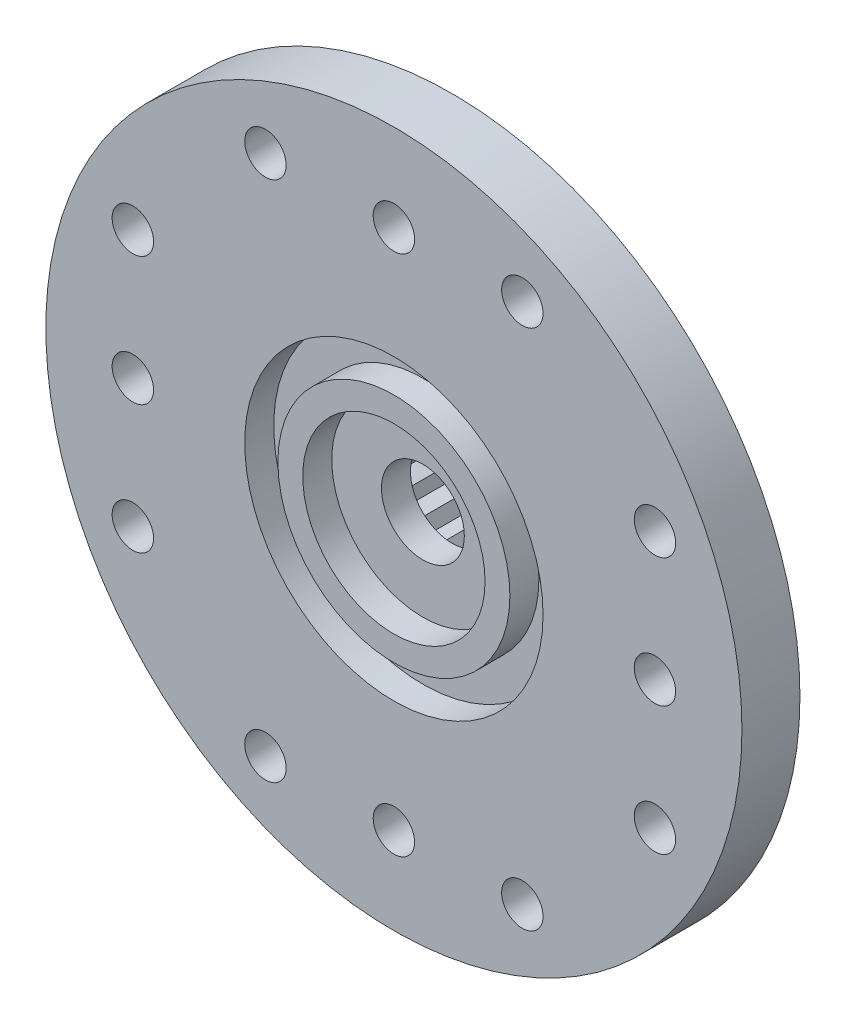
SolidWorks part; units mm, degrees
ref_plane "Front Plane" through (0, 0, 0) normal (0, 0, 1) x (1, 0, 0)
ref_plane "Top Plane" through (0, 0, 0) normal (0, 1, 0) x (1, 0, 0)
ref_plane "Right Plane" through (0, 0, 0) normal (1, 0, 0) x (0, 0, -1)
sketch "Sketch1" plane through (0, 0, 0) normal (0, 0, 1) x (1, 0, 0)
  line L50 (-10.25, 3) -> (-10.5946, 2.7283)
  line L51 (-10.5946, 2.7283) -> (-10.996, 2.9057)
  line L52 (-10.996, 2.9057) -> (-11.2623, 2.5569)
  line L53 (-11.2623, 2.5569) -> (-11.6952, 2.6289)
  line L54 (-11.6952, 2.6289) -> (-11.8664, 2.2248)
  line L55 (-11.8664, 2.2248) -> (-12.3036, 2.1869)
  line L56 (-12.3036, 2.1869) -> (-12.3689, 1.7529)
  line L57 (-12.3689, 1.7529) -> (-12.7829, 1.6075)
  line L58 (-12.7829, 1.6075) -> (-12.7382, 1.1709)
  line L59 (-12.7382, 1.1709) -> (-13.1031, 0.927)
  line L60 (-13.1031, 0.927) -> (-12.9512, 0.5153)
  line L61 (-12.9512, 0.5153) -> (-13.244, 0.1884)
  line L62 (-13.244, 0.1884) -> (-12.9945, -0.1727)
  line L63 (-12.9945, -0.1727) -> (-13.1968, -0.5621)
  line L64 (-13.1968, -0.5621) -> (-12.8654, -0.8498)
  line L65 (-12.8654, -0.8498) -> (-12.9644, -1.2773)
  line L66 (-12.9644, -1.2773) -> (-12.5719, -1.4735)
  line L67 (-12.5719, -1.4735) -> (-12.5615, -1.9123)
  line L68 (-12.5615, -1.9123) -> (-12.1325, -2.0047)
  line L69 (-12.1325, -2.0047) -> (-12.0133, -2.427)
  line L70 (-12.0133, -2.427) -> (-11.5748, -2.4098)
  line L71 (-11.5748, -2.4098) -> (-11.3543, -2.7893)
  line L72 (-11.3543, -2.7893) -> (-10.9339, -2.6636)
  line L73 (-10.9339, -2.6636) -> (-10.626, -2.9763)
  line L74 (-10.626, -2.9763) -> (-10.25, -2.75)
  line L75 (-10.25, -2.75) -> (-9.874, -2.9763)
  line L76 (-9.874, -2.9763) -> (-9.5661, -2.6636)
  line L77 (-9.5661, -2.6636) -> (-9.1456, -2.7893)
  line L78 (-9.1456, -2.7893) -> (-8.9251, -2.4098)
  line L79 (-8.9251, -2.4098) -> (-8.4866, -2.427)
  line L80 (-8.4866, -2.427) -> (-8.3675, -2.0047)
  line L81 (-8.3675, -2.0047) -> (-7.9384, -1.9123)
  line L82 (-7.9384, -1.9123) -> (-7.9281, -1.4735)
  line L83 (-7.9281, -1.4735) -> (-7.5355, -1.2773)
  line L84 (-7.5355, -1.2773) -> (-7.6346, -0.8498)
  line L85 (-7.6346, -0.8498) -> (-7.3031, -0.5621)
  line L86 (-7.3031, -0.5621) -> (-7.5054, -0.1727)
  line L87 (-7.5054, -0.1727) -> (-7.2559, 0.1884)
  line L88 (-7.2559, 0.1884) -> (-7.5487, 0.5153)
  line L89 (-7.5487, 0.5153) -> (-7.3968, 0.927)
  line L90 (-7.3968, 0.927) -> (-7.7617, 1.1709)
  line L91 (-7.7617, 1.1709) -> (-7.717, 1.6075)
  line L92 (-7.717, 1.6075) -> (-8.1311, 1.7529)
  line L93 (-8.1311, 1.7529) -> (-8.1963, 2.1869)
  line L94 (-8.1963, 2.1869) -> (-8.6336, 2.2248)
  line L95 (-8.6336, 2.2248) -> (-8.8047, 2.6289)
  line L96 (-8.8047, 2.6289) -> (-9.2376, 2.5569)
  line L97 (-9.2376, 2.5569) -> (-9.5039, 2.9057)
  line L98 (-9.5039, 2.9057) -> (-9.9053, 2.7283)
  line L99 (-9.9053, 2.7283) -> (-10.25, 3)
  line L100 (-10.25, 3) -> (-10.5946, 2.7283)
  line L101 (-10.5946, 2.7283) -> (-10.996, 2.9057)
  line L102 (-10.996, 2.9057) -> (-11.2623, 2.5569)
  line L103 (-11.2623, 2.5569) -> (-11.6952, 2.6289)
  line L104 (-11.6952, 2.6289) -> (-11.8664, 2.2248)
  line L105 (-11.8664, 2.2248) -> (-12.3036, 2.1869)
  line L106 (-12.3036, 2.1869) -> (-12.3689, 1.7529)
  line L107 (-12.3689, 1.7529) -> (-12.7829, 1.6075)
  line L108 (-12.7829, 1.6075) -> (-12.7382, 1.1709)
  line L109 (-12.7382, 1.1709) -> (-13.1031, 0.927)
  line L110 (-13.1031, 0.927) -> (-12.9512, 0.5153)
  line L111 (-12.9512, 0.5153) -> (-13.244, 0.1884)
  line L112 (-13.244, 0.1884) -> (-12.9945, -0.1727)
  line L113 (-12.9945, -0.1727) -> (-13.1968, -0.5621)
  line L114 (-13.1968, -0.5621) -> (-12.8654, -0.8498)
  line L115 (-12.8654, -0.8498) -> (-12.9644, -1.2773)
  line L116 (-12.9644, -1.2773) -> (-12.5719, -1.4735)
  line L117 (-12.5719, -1.4735) -> (-12.5615, -1.9123)
  line L118 (-12.5615, -1.9123) -> (-12.1325, -2.0047)
  line L119 (-12.1325, -2.0047) -> (-12.0133, -2.427)
  line L120 (-12.0133, -2.427) -> (-11.5748, -2.4098)
  line L121 (-11.5748, -2.4098) -> (-11.3543, -2.7893)
  line L122 (-11.3543, -2.7893) -> (-10.9339, -2.6636)
  line L123 (-10.9339, -2.6636) -> (-10.626, -2.9763)
  line L124 (-10.626, -2.9763) -> (-10.25, -2.75)
  line L125 (-10.25, -2.75) -> (-9.874, -2.9763)
  line L126 (-9.874, -2.9763) -> (-9.5661, -2.6636)
  line L127 (-9.5661, -2.6636) -> (-9.1456, -2.7893)
  line L128 (-9.1456, -2.7893) -> (-8.9251, -2.4098)
  line L129 (-8.9251, -2.4098) -> (-8.4866, -2.427)
  line L130 (-8.4866, -2.427) -> (-8.3675, -2.0047)
  line L131 (-8.3675, -2.0047) -> (-7.9384, -1.9123)
  line L132 (-7.9384, -1.9123) -> (-7.9281, -1.4735)
  line L133 (-7.9281, -1.4735) -> (-7.5355, -1.2773)
  line L134 (-7.5355, -1.2773) -> (-7.6346, -0.8498)
  line L135 (-7.6346, -0.8498) -> (-7.3031, -0.5621)
  line L136 (-7.3031, -0.5621) -> (-7.5054, -0.1727)
  line L137 (-7.5054, -0.1727) -> (-7.2559, 0.1884)
  line L138 (-7.2559, 0.1884) -> (-7.5487, 0.5153)
  line L139 (-7.5487, 0.5153) -> (-7.3968, 0.927)
  line L140 (-7.3968, 0.927) -> (-7.7617, 1.1709)
  line L141 (-7.7617, 1.1709) -> (-7.717, 1.6075)
  line L142 (-7.717, 1.6075) -> (-8.1311, 1.7529)
  line L143 (-8.1311, 1.7529) -> (-8.1963, 2.1869)
  line L144 (-8.1963, 2.1869) -> (-8.6336, 2.2248)
  line L145 (-8.6336, 2.2248) -> (-8.8047, 2.6289)
  line L146 (-8.8047, 2.6289) -> (-9.2376, 2.5569)
  line L147 (-9.2376, 2.5569) -> (-9.5039, 2.9057)
  line L148 (-9.5039, 2.9057) -> (-9.9053, 2.7283)
  line L149 (-9.9053, 2.7283) -> (-10.25, 3)
  circle A0 centre (-10.25, 0) radius 4.5
  dimension "D2" = 9
  dimension "D1" = 0
extrude "Boss-Extrude1" add sketch "Sketch1" against normal blind 3.75 contours A0 L149 L148 L147 L146 L145 L144 L143 L142 L141 L140 L139 L138 L137 L136 L135 L134 L133 L132 L131 L130 L129 L128 L127 L126 L125 L124 L123 L122 L121 L120 L119 L118 L117 L116 L115 L114 L113 L112 L111 L110 L109 L108 L107 L106 L105 L104 L103 L102 L101
sketch "Sketch2" plane through (0, 0, 0) normal (0, 0, 1) x (1, 0, 0)
  circle A0 centre (-10.25, 0) radius 1.25
  circle A1 centre (-10.25, 0) radius 3.5
  circle A2 centre (-10.25, 0) radius 4.5
  dimension "D1" = 7
  dimension "D2" = 2.5
  dimension "D3" = 9
extrude "Boss-Extrude2" add sketch "Sketch2" along normal blind 1.75 contours A2 A1 | A1 A0
sketch "Sketch4" plane through (0, 0, 1.75) normal (0, 0, 1) x (1, 0, 0)
  circle A0 centre (-10.25, 0) radius 3.5
  circle A1 centre (-10.25, 0) radius 2.75
  circle M2 centre (-10.25, 0) radius 1.25
  dimension "D1" = 7
  dimension "D2" = 0.75
extrude "Cut-Extrude1" cut sketch "Sketch4" against normal blind 0.875 contours A1 M2
sketch "Sketch6" plane through (0, 0, 1.75) normal (0, 0, 1) x (1, 0, 0)
  circle A0 centre (-10.25, 0) radius 3.5
  circle A1 centre (-10.25, 0) radius 2.75 construction
  circle A2 centre (-10.25, 0) radius 4.5
  circle M2 centre (-10.25, 0) radius 4.5
  dimension "D1" = 0.75
  dimension "D2" = 9
extrude "Cut-Extrude2" cut sketch "Sketch6" against normal blind 0.875 contours A0 M2
sketch "Sketch7" plane through (0, 0, 1.75) normal (0, 0, 1) x (1, 0, 0)
  circle A0 centre (-10.25, 0) radius 10.5
  circle A1 centre (-10.25, 0) radius 4.5
  dimension "D1" = 21
extrude "Boss-Extrude3" add sketch "Sketch7" against normal blind 1.75
sketch "Sketch9" plane through (0, 0, 1.75) normal (0, 0, 1) x (1, 0, 0)
  line L0 (-10.25, 0) -> (-10.25, 11.6833) construction
  circle A0 centre (-10.25, 7.875) radius 0.625
  circle A1 centre (-14.125, 7.875) radius 0.625
  circle A2 centre (-10.25, 0) radius 10.5 construction
  circle A3 centre (-6.375, 7.875) radius 0.625
  dimension "D1" = 2
  dimension "D2" = 1.25
  dimension "D3" = 1.25
  dimension "D4" = 2.625
extrude "Cut-Extrude3" cut sketch "Sketch9" against normal through all
pattern_circular "CirPattern1" count 4 over 360 about axis through (-10.25, 0, 0) along (0, 0, 1) of "Cut-Extrude3"
chamfer "Chamfer1" distance 1 angle 30 1 edges at (-5.75, 0, 0)
sketch "Sketch10" [suppressed] plane through (0, 0, 1.75) normal (0, 0, 1) x (1, 0, 0)
  line L0 (-10.25, 0) -> (-10.25, 9.0053) construction
  line L1 (-10.25, 0) -> (0.0732, 10.3232) construction
  line L2 (-10.25, 0) -> (1.1009, 0) construction
  line L3 (-8.0869, 17.7016) -> (-6.0299, 6.622)
  line L4 (-3.6279, 4.2201) -> (7.4516, 2.163)
  line L5 (7.4516, -2.163) -> (-3.6279, -4.2201)
  line L6 (-6.0299, -6.622) -> (-8.0869, -17.7016)
  line L7 (-12.413, -17.7016) -> (-14.47, -6.622)
  line L8 (-16.872, -4.2201) -> (-27.9515, -2.163)
  line L9 (-27.9515, 2.163) -> (-16.872, 4.2201)
  line L10 (-14.47, 6.622) -> (-12.413, 17.7016)
  arc A0 (-8.0869, 17.7016) -> (-10.25, 19.5) centre (-10.25, 17.3) ccw
  arc A1 (7.4516, -2.163) -> (7.4516, 2.163) centre (7.05, 0) ccw
  arc A2 (-6.0299, 6.622) -> (-3.6279, 4.2201) centre (-3.0803, 7.1697) ccw
  circle A3 centre (-10.25, 15.875) radius 0.625
  circle A4 centre (-10.25, 12.875) radius 0.625
  circle A5 centre (-10.25, 9.875) radius 0.625
  circle A6 centre (-10.25, 6.875) radius 0.625
  arc A7 (7.4516, -2.163) -> (9.25, 0) centre (7.05, 0) ccw
  circle A8 centre (5.625, 0) radius 0.625
  circle A9 centre (2.625, 0) radius 0.625
  circle A10 centre (-0.375, 0) radius 0.625
  circle A11 centre (-3.375, 0) radius 0.625
  arc A12 (-3.6279, -4.2201) -> (-6.0299, -6.622) centre (-3.0803, -7.1697) ccw
  arc A13 (-12.413, -17.7016) -> (-8.0869, -17.7016) centre (-10.25, -17.3) ccw
  arc A14 (-12.413, -17.7016) -> (-10.25, -19.5) centre (-10.25, -17.3) ccw
  circle A15 centre (-10.25, -15.875) radius 0.625
  circle A16 centre (-10.25, -12.875) radius 0.625
  circle A17 centre (-10.25, -9.875) radius 0.625
  circle A18 centre (-10.25, -6.875) radius 0.625
  arc A19 (-14.47, -6.622) -> (-16.872, -4.2201) centre (-17.4196, -7.1697) ccw
  arc A20 (-27.9515, 2.163) -> (-27.9515, -2.163) centre (-27.5499, 0) ccw
  arc A21 (-27.9515, 2.163) -> (-29.7499, 0) centre (-27.5499, 0) ccw
  circle A22 centre (-26.1249, 0) radius 0.625
  circle A23 centre (-23.1249, 0) radius 0.625
  circle A24 centre (-20.1249, 0) radius 0.625
  circle A25 centre (-17.1249, 0) radius 0.625
  arc A26 (-16.872, 4.2201) -> (-14.47, 6.622) centre (-17.4196, 7.1697) ccw
  arc A27 (-8.0869, 17.7016) -> (-12.413, 17.7016) centre (-10.25, 17.3) ccw
  circle A28 centre (-10.25, 0) radius 4.5
  point P1 (-10.25, 0)
  point P10 (-5.6538, 4.5962)
  point P20 (-5.6538, 4.5962)
  point P21 (-10.25, 19.5)
  point P84 (-10.25, 0)
  circle M4 centre (-10.25, 0) radius 3.5
  dimension "D2" = 19.5
  dimension "D3" = 19.5
  dimension "D4" = 4.4
  dimension "D5" = 4.4
  dimension "D7" = 3
  dimension "D8" = 1.25
  dimension "D9" = 3
  dimension "D1" = 45
  dimension "D6" = 6.5
  dimension "D10" = 4
  dimension "D11" = 4
extrude "Boss-Extrude4" [suppressed] add sketch "Sketch10" against normal blind 1.75 contours A0 A27 L10 A26 L9 A20 L8 A19 L7 A13 L6 A12 L5 A1 L4 A2 L3 A3 A4 A5 A6 A8 A9 A10 A11 A15 A16 A17 A18 A22 A23 M4
chamfer "Chamfer2" [suppressed] distance 1 angle 30
sketch "Sketch11" [suppressed] plane through (0, 0, 1.75) normal (0, 0, 1) x (1, 0, 0)
  line L0 (-10.25, 0) -> (-10.25, 17.5605) construction
  line L1 (-10.25, 0) -> (4.9579, 8.7803) construction
  line L2 (-10.25, 0) -> (4.9579, -8.7803) construction
  line L3 (-10.25, 0) -> (-10.25, -17.5605) construction
  line L4 (-10.25, 0) -> (-25.4578, -8.7803) construction
  line L5 (-10.25, 0) -> (-25.4578, 8.7803) construction
  line L6 (-10.25, 0) -> (-3.969, 10.8789) construction
  line L7 (-10.25, 0) -> (2.312, 0) construction
  line L8 (-10.25, 0) -> (-3.969, -10.8789) construction
  line L9 (-10.25, 0) -> (-16.5309, -10.8789) construction
  line L10 (-10.25, 0) -> (-22.8119, 0) construction
  line L11 (-10.25, 0) -> (-16.5309, 10.8789) construction
  line L12 (-8.5769, 14.5133) -> (-6.25, 6.9282)
  line L13 (-6.25, 6.9282) -> (1.4824, 8.7055)
  line L14 (3.1554, 5.8077) -> (-2.25, 0)
  line L15 (-2.25, 0) -> (3.1554, -5.8077)
  line L16 (1.4824, -8.7055) -> (-6.25, -6.9282)
  line L17 (-6.25, -6.9282) -> (-8.5769, -14.5133)
  line L18 (-11.923, -14.5133) -> (-14.25, -6.9282)
  line L19 (-14.25, -6.9282) -> (-21.9823, -8.7055)
  line L20 (-23.6553, -5.8077) -> (-18.25, 0)
  line L21 (-18.25, 0) -> (-23.6553, 5.8077)
  line L22 (-21.9823, 8.7055) -> (-14.25, 6.9282)
  line L23 (-14.25, 6.9282) -> (-11.923, 14.5133)
  circle A0 centre (-10.25, 0) radius 4.5
  arc A1 (-8.5769, 14.5133) -> (-10.25, 15.75) centre (-10.25, 14) ccw
  arc A2 (3.3899, 7.875) -> (1.4824, 8.7055) centre (1.8744, 7) ccw
  circle A4 centre (-10.25, 13.375) radius 0.625
  circle A5 centre (-10.25, 10.375) radius 0.625
  circle A6 centre (-10.25, 7.375) radius 0.625
  circle A7 centre (1.3331, 6.6875) radius 0.625
  arc A8 (3.1554, 5.8077) -> (3.3899, 7.875) centre (1.8744, 7) ccw
  circle A9 centre (-1.2649, 5.1875) radius 0.625
  circle A10 centre (-3.863, 3.6875) radius 0.625
  arc A11 (3.3899, -7.875) -> (3.1554, -5.8077) centre (1.8744, -7) ccw
  circle A12 centre (1.3331, -6.6875) radius 0.625
  arc A13 (1.4824, -8.7055) -> (3.3899, -7.875) centre (1.8744, -7) ccw
  circle A14 centre (-1.2649, -5.1875) radius 0.625
  circle A15 centre (-3.863, -3.6875) radius 0.625
  arc A16 (-10.25, -15.75) -> (-8.5769, -14.5133) centre (-10.25, -14) ccw
  circle A17 centre (-10.25, -13.375) radius 0.625
  arc A18 (-11.923, -14.5133) -> (-10.25, -15.75) centre (-10.25, -14) ccw
  circle A19 centre (-10.25, -10.375) radius 0.625
  circle A20 centre (-10.25, -7.375) radius 0.625
  arc A21 (-23.8899, -7.875) -> (-21.9823, -8.7055) centre (-22.3743, -7) ccw
  circle A22 centre (-21.833, -6.6875) radius 0.625
  arc A23 (-23.6553, -5.8077) -> (-23.8899, -7.875) centre (-22.3743, -7) ccw
  circle A24 centre (-19.235, -5.1875) radius 0.625
  circle A25 centre (-16.6369, -3.6875) radius 0.625
  arc A26 (-23.8899, 7.875) -> (-23.6553, 5.8077) centre (-22.3743, 7) ccw
  circle A27 centre (-21.833, 6.6875) radius 0.625
  arc A28 (-21.9823, 8.7055) -> (-23.8899, 7.875) centre (-22.3743, 7) ccw
  circle A29 centre (-19.235, 5.1875) radius 0.625
  circle A30 centre (-16.6369, 3.6875) radius 0.625
  arc A31 (-10.25, 15.75) -> (-11.923, 14.5133) centre (-10.25, 14) ccw
  point P5 (-10.25, 0)
  point P12 (-10.25, 0)
  point P20 (-10.25, 0)
  point P22 (-6.25, 6.9282)
  point P26 (-10.25, 15.75)
  point P27 (3.3899, 7.875)
  point P102 (-10.25, 0)
  dimension "D4" = 15.75
  dimension "D5" = 15.75
  dimension "D6" = 3.5
  dimension "D7" = 3.5
  dimension "D9" = 1.25
  dimension "D10" = 1.75
  dimension "D2" = 30
  dimension "D8" = 8
  dimension "D11" = 3
  dimension "D1" = 6
  dimension "D3" = 6
  dimension "D12" = 6
extrude "Boss-Extrude5" [suppressed] add sketch "Sketch11" against normal blind 1.75 contours A1 A31 L23 L22 A28 A26 L21 L20 A23 A21 L19 L18 A18 A16 L17 L16 A13 A11 L15 L14 A8 A2 L13 L12 A0 A4 A5 A6 A7 A9 A10 A12 A14 A15 A17 A19 A20
chamfer "Chamfer4" [suppressed] distance 1 angle 30
sketch "Sketch12" [suppressed] plane through (0, 0, 0.875) normal (0, 0, 1) x (1, 0, 0)
  circle A0 centre (-10.25, 0) radius 1.25
  circle A1 centre (-10.25, 0) radius 5
extrude "Boss-Extrude6" [suppressed] add sketch "Sketch12" along normal blind 0.125
sketch "Sketch14" [suppressed] plane through (0, 0, 1) normal (0, 0, 1) x (1, 0, 0)
  line L0 (-10.25, 0) -> (-28.2499, 0) construction
  line L1 (-10.25, -6) -> (-28.2499, -6)
  line L2 (-10.25, 6) -> (-28.2499, 6)
  arc A0 (-10.25, -6) -> (-10.25, 6) centre (-10.25, 0) ccw
  arc A1 (-28.2499, 6) -> (-28.2499, -6) centre (-28.2499, 0) ccw
  point P4 (-19.2499, 0)
  dimension "D1" = 12
  dimension "D2" = 29.9999
extrude "Boss-Extrude7" [suppressed] add sketch "Sketch14" along normal blind 3
sketch "Sketch16" [suppressed] plane through (0, 0, 1) normal (0, 0, -1) x (-1, 0, 0)
  line L0 (25.9999, 0) -> (30.4999, 0) construction
  line L1 (25.9999, 2.75) -> (30.4999, 2.75)
  line L2 (25.9999, -2.75) -> (30.4999, -2.75)
  arc A0 (25.9999, 2.75) -> (25.9999, -2.75) centre (25.9999, 0) ccw
  arc A1 (30.4999, -2.75) -> (30.4999, 2.75) centre (30.4999, 0) ccw
  arc A10 (28.2499, -6) -> (28.2499, 6) centre (28.2499, 0) ccw construction
  point P3 (28.2499, 0)
  point P8 (34.2499, 0)
  point P9 (33.2499, 0)
  dimension "D2" = 10
  dimension "D3" = 1
  dimension "D1" = 5.5
extrude "Boss-Extrude8" [suppressed] add sketch "Sketch16" along normal blind 2.75 contours L1 A1 L2 A0
sketch "Sketch17" [suppressed] plane through (0, 0, -1.75) normal (0, 0, -1) x (-1, 0, 0)
  circle A0 centre (30.7499, 0) radius 1.5
  circle A1 centre (25.7499, 0) radius 1.5
  arc A5 (28.2499, -6) -> (28.2499, 6) centre (28.2499, 0) ccw construction
  dimension "D1" = 3
  dimension "D2" = 3
  dimension "D3" = 2
  dimension "D4" = 2
extrude "Cut-Extrude4" [suppressed] cut sketch "Sketch17" against normal through all
sketch "Sketch18" [suppressed] plane through (0, 0, 1) normal (0, 0, -1) x (-1, 0, 0)
  circle A0 centre (10.25, 0) radius 3
  dimension "D1" = 6
extrude "Cut-Extrude5" [suppressed] cut sketch "Sketch18" against normal through all
sketch "Sketch19" [suppressed] plane through (0, 0, 1.5) normal (0, 0, 1) x (1, 0, 0)
  line L0 (-35.7499, 0) -> (15.25, 0) construction
  line L1 (-9.625, 5.9674) -> (14.1146, 3.481)
  line L2 (14.1146, -3.481) -> (-9.625, -5.9674)
  line L3 (-10.25, 0) -> (-10.25, 10.691) construction
  line L4 (-34.6145, -3.481) -> (-10.875, -5.9674)
  line L5 (-10.875, 5.9674) -> (-34.6145, 3.481)
  circle A0 centre (-10.25, 0) radius 6
  arc A1 (14.1146, -3.481) -> (14.1146, 3.481) centre (13.75, 0) ccw
  circle A2 centre (14.625, 0) radius 0.625
  circle A3 centre (11.375, 0) radius 0.625
  circle A4 centre (8.125, 0) radius 0.625
  circle A5 centre (4.875, 0) radius 0.625
  circle A6 centre (1.625, 0) radius 0.625
  circle A7 centre (-22.1249, 0) radius 0.625
  circle A8 centre (-25.3749, 0) radius 0.625
  circle A9 centre (-28.6249, 0) radius 0.625
  circle A10 centre (-31.8749, 0) radius 0.625
  circle A11 centre (-35.1249, 0) radius 0.625
  arc A12 (-34.6145, -3.481) -> (-34.6145, 3.481) centre (-34.2499, 0) cw
  point P37 (-10.25, -6)
  circle M5 centre (-10.25, 0) radius 5
  circle M6 centre (-10.25, 0) radius 1.25
  dimension "D1" = 12
  dimension "D2" = 7
  dimension "D4" = 1.25
  dimension "D5" = 2
  dimension "D3" = 27.4999
  dimension "D6" = 5
extrude "Boss-Extrude9" [suppressed] add sketch "Sketch19" along normal blind 2.5 contours A12 L4 A0 L5 A10 A8 A7 A9 A11 | A0 M5 | M5 M6 | L2 A1 L1 A0 A6 A5 A4 A3 A2
sketch "Sketch20" [suppressed] plane through (0, 0, 4) normal (0, 0, 1) x (1, 0, 0)
  arc A0 (-9.625, 5.9674) -> (-10.875, 5.9674) centre (-10.25, 0) ccw construction
  circle A1 centre (-10.25, 0) radius 4
  circle A2 centre (-10.25, 0) radius 6
  point P5 (-10.25, 4)
  point P7 (-10.25, -4)
  dimension "D1" = 2
extrude "Boss-Extrude10" [suppressed] add sketch "Sketch20" along normal blind 1
sketch "Sketch21" [suppressed] plane through (0, 0, 4) normal (0, 0, 1) x (1, 0, 0)
  circle A0 centre (-10.25, 0) radius 4 construction
  circle A1 centre (-10.25, 0) radius 4
  circle A2 centre (-10.25, 0) radius 3.25
  dimension "D1" = 0.75
extrude "Boss-Extrude11" [suppressed] add sketch "Sketch21" along normal offset from surface (0.5 mm away) 0.5
sketch "Sketch22" [suppressed] plane through (0, 0, 4) normal (0, 0, 1) x (1, 0, 0)
  circle A0 centre (-10.25, 0) radius 3.25
extrude "Cut-Extrude6" [suppressed] cut sketch "Sketch22" against normal offset from surface (3 mm away) 1 contours A0
chamfer "Chamfer5" [suppressed] distance 0.75 angle 45
ref_plane "Plane1" [suppressed] through (0, 4.5, 0) normal (0, 1, 0) x (1, 0, 0)
ref_plane "Plane3" [suppressed] through (0, 0.5, 0) normal (0, 1, 0) x (1, 0, 0)
sketch "Sketch26" [suppressed] plane through (0, 0.5, 0) normal (0, 1, 0) x (1, 0, 0)
  line L0 (-17.4408, -4) -> (-16.1908, -5)
  line L1 (-10.875, -4) -> (-34.6145, -4) construction
  line L2 (-16.1908, -5) -> (-15.6228, -4)
  line L3 (-15.6228, -4) -> (-17.4408, -4)
  line L4 (-16.25, -5) -> (-4.25, -5) construction
  dimension "D1" = 1.25
extrude "Boss-Extrude15" [suppressed] add sketch "Sketch26" against normal blind 1
ref_plane "Plane4" [suppressed] through (0, 5, 0) normal (0, 1, 0) x (1, 0, 0)
sketch "Sketch27" [suppressed] plane through (0, 5, 0) normal (0, 1, 0) x (1, 0, 0)
  line L0 (-17.4408, -4) -> (-13.2508, -4)
  line L1 (-16.1908, -5) -> (-13.2508, -5)
  line L3 (-17.4408, -4) -> (-16.1908, -5)
  line L4 (-16.1908, -5) -> (-15.6228, -4)
  line L5 (-15.6228, -4) -> (-17.4408, -4)
  line L6 (-17.4408, -4) -> (-16.1908, -5)
  line L10 (-13.2508, -5) -> (-13.2508, -4)
  dimension "D1" = 0
extrude "Boss-Extrude16" [suppressed] add sketch "Sketch27" against normal blind 1 contours L6 L1 L10 L0
mirror "Mirror1" [suppressed] about plane through (0, 0, 0) normal (0, 1, 0)
ref_plane "Plane5" [suppressed] through (-10.25, 0, 0) normal (1, 0, 0) x (0, 0, -1)
mirror "Mirror2" [suppressed] about plane through (-10.25, 0, 0) normal (1, 0, 0)
ref_plane "Plane6" [suppressed] through (0, 0, 2.75) normal (0, 0, 1) x (1, 0, 0)
mirror "Mirror3" [suppressed] about plane through (0, 0, 2.75) normal (0, 0, 1)
mirror "Mirror4" [suppressed] about plane through (-10.25, 0, 0) normal (1, 0, 0)
sketch "Sketch29" [suppressed] plane through (0, -5, 0) normal (0, -1, 0) x (1, 0, 0)
  line L0 (-15.25, 1.5) -> (-5.25, 1.5) construction
  line L1 (-13.2508, 0.5) -> (-7.2491, 0.5)
  line L2 (-13.2508, 0.5) -> (-13.2508, 1.5)
  line L3 (-13.2508, 1.5) -> (-7.2491, 1.5)
  line L4 (-7.2491, 0.5) -> (-7.2491, 1.5)
  line L5 (-7.2491, 0.5) -> (-7.2491, 1.5) construction
extrude "Boss-Extrude17" [suppressed] add sketch "Sketch29" against normal up to surface (1 mm away)
sketch "Sketch31" [suppressed] plane through (0, 0, 5) normal (0, 0, 1) x (1, 0, 0)
  line L1 (-19.5679, -7.6233) -> (-0.9321, -7.6233)
  line L2 (-19.5679, -7.6233) -> (-19.5679, 7.6233)
  line L3 (-19.5679, 7.6233) -> (-0.9321, 7.6233)
  line L4 (-0.9321, -7.6233) -> (-0.9321, 7.6233)
  line L5 (-19.5679, -7.6233) -> (-0.9321, 7.6233) construction
  line L6 (-19.5679, 7.6233) -> (-0.9321, -7.6233) construction
  point P0 (-10.25, 0)
  point P1 (-10.25, 0)
extrude "Cut-Extrude7" [suppressed] cut sketch "Sketch31" against normal blind 0.7493
ref_plane "Plane7" [suppressed] through (-10.25, 0, 0) normal (1, 0, 0) x (0, 0, -1)
